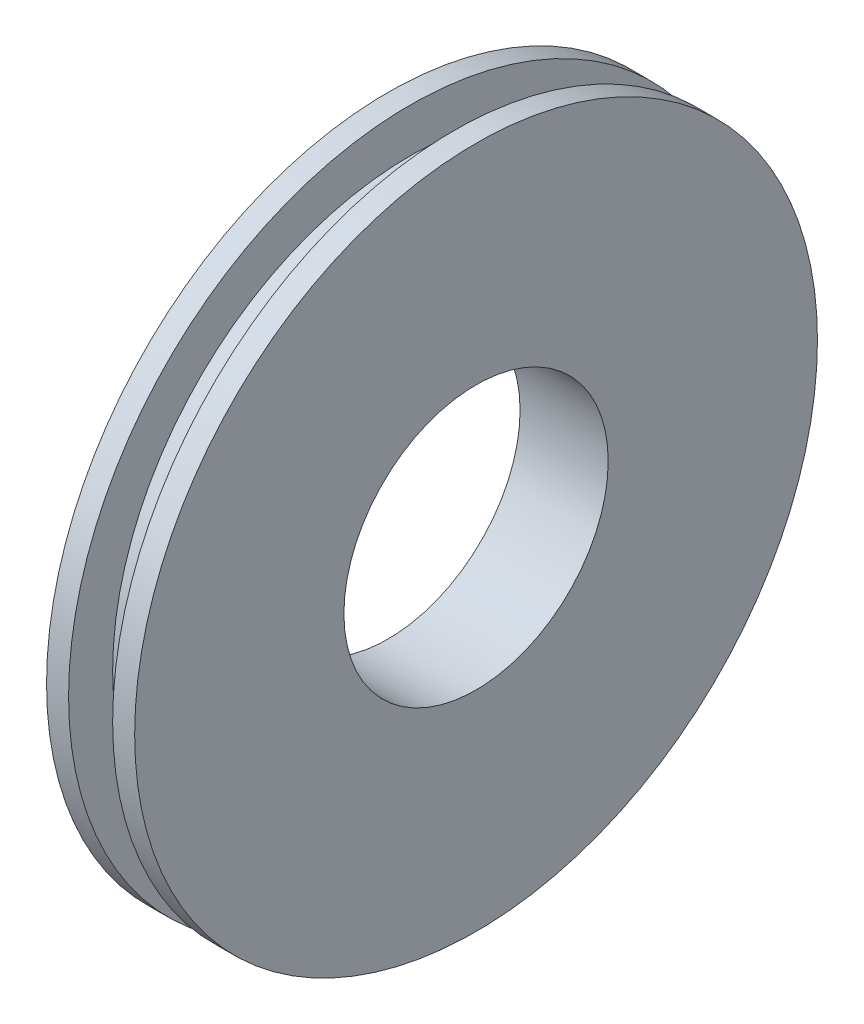
SolidWorks part; units mm, degrees
ref_plane "Ebene vorne" through (0, 0, 0) normal (0, 0, 1) x (1, 0, 0)
ref_plane "Ebene oben" through (0, 0, 0) normal (0, 1, 0) x (1, 0, 0)
ref_plane "Ebene rechts" through (0, 0, 0) normal (1, 0, 0) x (0, 0, -1)
sketch "Skizze1" plane through (0, 0, 0) normal (0, 0, 1) x (1, 0, 0)
  line L0 (0, 66.0424) -> (0, -61.688) construction
  line L1 (-47.5764, 0) -> (61.7686, 0) construction
  line L2 (1, 3) -> (-1, 3)
  line L3 (-1, 3) -> (-1, 7.75)
  line L4 (-1, 7.75) -> (-0.5, 7.75)
  line L5 (-0.5, 7.75) -> (-0.5, 6.75)
  line L6 (-0.5, 6.75) -> (0.5, 6.75)
  line L7 (1, 3) -> (1, 7.75)
  line L8 (1, 7.75) -> (0.5, 7.75)
  line L9 (0.5, 7.75) -> (0.5, 6.75)
  point P5 (-1, 5.375)
  point P13 (0, 3)
  point P16 (0, 6.75)
  dimension "D1" = 7.75
  dimension "D2" = 6.75
  dimension "D3" = 1
  dimension "D4" = 0.5
  dimension "D6" = 3
revolve "Rotation1" add sketch "Skizze1" angle 360 about L1
equation "\"joint-dowel diameter\"= 3"
equation "\"tendon-dowel diameter\" = 2"
equation "\"tendon-dowel bed wall thickness\" = 1.5"
equation "\"gap width\"= 0.5"
equation "\"printing extra gap\" = 0.2"
equation "\"DIP length\"= 24"
equation "\"DIP hight\"= 15"
equation "\"DIP width\"= 18"
equation "\"pulley width\"= 2"
equation "\"joint folk inner width\" = 2"
equation "\"tendon-dowel length\" = 6"
equation "\"D3@Skizze1\"=\"pulley width\"/2"
equation "\"D6@Skizze1\"=\"pulley inner diameter\"/2 "
equation "\"joint-dowel length\"= 14"
equation "\"PIP length\" = 26"
equation "\"PIP height\" = \"DIP hight\" + 1"
equation "\"PIP width\"= \"DIP width\""
equation "\"MCP length\" = 42"
equation "\"MCP height\" = \"PIP height\" + 1.5"
equation "\"MCP width\"= \"DIP width\""
equation "\"DIP: pulley outer diameter\"= \"DIP hight\" - \"pulley-frame-gap\""
equation "\"DIP: pulley inner diameter\"= \"DIP: pulley outer diameter\" - 2*\"pulley-wall-height\""
equation "\"PIP: pulley outer diameter\"= \"PIP height\" - \"pulley-frame-gap\""
equation "\"PIP: pulley inner diameter\"= \"PIP: pulley outer diameter\" - 2*\"pulley-wall-height\""
equation "\"MCP: pulley outer diameter\"= \"MCP: pulley inner diameter\" + 4"
equation "\"MCP: pulley inner diameter\"= 12"
equation "\"joint-folk inner depth\" = 15.3"
equation "\"tendon-shaft diameter\" = 1.5"
equation "\"tendon-fixation-gap diameter\" = 4"
equation "\"tendon-fixation-gap depth\" = 2.5"
equation "\"tendon-shaft-fixation distance\" = \"tendon-fixation-gap depth\" - \"tendon-shaft diameter\"/2"
equation "\"D2@Skizze1\"=\"PIP: pulley inner diameter\"/2"
equation "\"D1@Skizze1\"=\"PIP: pulley outer diameter\"/2"
equation "\"pulley-frame-gap\" = 0.5"
equation "\"pulley-wall-height\" = 1"
equation "\"joint-limb-gap\" = 1"
equation "\"joint-dowel diameter 2\" = 2"
equation "\"joint-dowel groove height\" = 1"
equation "\"joint-bearing inner-diameter\" = 3"
equation "\"joint-bearing outer-diameter 1\" = 6"
equation "\"joint-bearing outer-diameter 2\" = 7.2"
equation "\"joint-bearing width\" = 2"
equation "\"joint-bearing flange\" = 0.6"
equation "\"pulley tendon ground width\" = 1"
equation "\"MCP2: joint-folk-height down\"= 1.5"
equation "\"MCP2: joint-folk-height up\"= 3.0"
equation "\"MCP2: pulley width\" = 3"
equation "\"MCP2: pulley inner diameter\"= 6"
equation "\"MCP2: pulley gap\" = 0.5"
equation "\"joint-folk-outer width left\" = 3.5"
equation "\"joint-folk-outer width right\" = 5"
equation "\"rubber-band-height\" = 1"
equation "\"rubber-band-width\" = 2"
equation "\"rubber-band-fix-pit width\" = 2.5"
equation "\"rubber-band-fix-pit height\" = 1.2"
equation "\"rubber-band-fix-pit inner-x-border-distance\" = 3.5"
equation "\"rubber-band-fix-pit surface-x-border-distance\" = 1"
equation "\"rubber-band-fix-pin diameter\" = 1"
equation "\"rubber-band-fix-pin length\" = 6"
equation "\"cable-width\" = 3.5"
equation "\"cable-height\" = 1"
equation "\"encoder-electr-width\" = 6 + \"printing extra gap\""
equation "\"encoder-electr-length head\" = 5 + \"printing extra gap\"/2"
equation "\"encoder-electr-length bottom\" = 10 + \"printing extra gap\"/2"
equation "\"encoder-electr-height\" = 2 + \"printing extra gap\""
equation "\"encoder-electr-thickness wall\" = 0.5"
equation "\"limb-fix-screw outer diameter\" = 4"
equation "\"limb-fix-screw inner diameter\" = 1.9"
equation "\"limb-fix-screw outer depth\" = 2"
equation "\"limb-fix-screw thread surface distance\" = 2"
equation "\"encoder-magnet diameter\" = 2"
equation "\"encoder-magnet length\" = 4"
equation "\"tendon-metal-sleeve inner diameter\" = \"tendon-shaft diameter\""
equation "\"tendon-metal-sleeve outer diameter\" = \"tendon-shaft diameter\" + 1"
equation "\"tendon-metal-sleeve flange diameter\" = \"tendon-metal-sleeve outer diameter\" + 2"
equation "\"tendon-metal-sleeve length\" = 3"
equation "\"tendon-metal-sleeve flange length\" = 0.5"
equation "\"D4@Skizze1\"=\"pulley tendon ground width\"/2"
equation "\"pulley inner diameter\" = 6"
